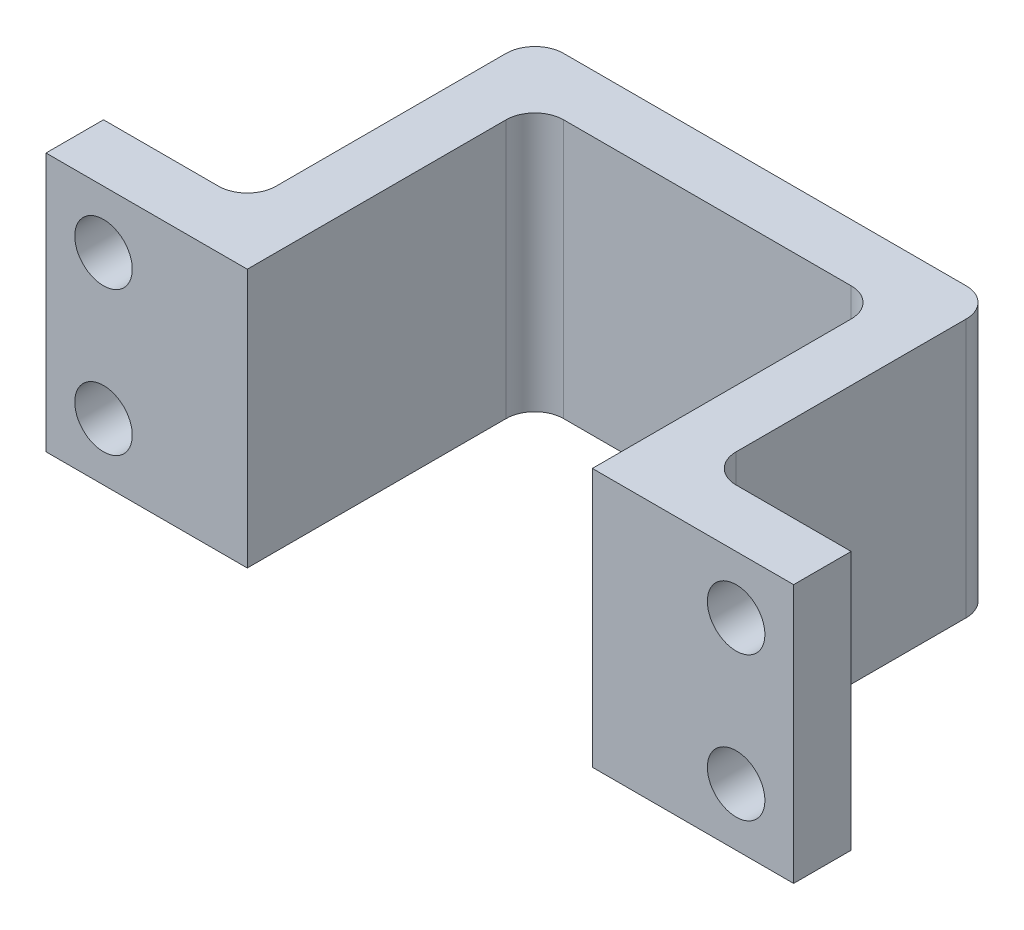
SolidWorks part; units mm, degrees
ref_plane "Front Plane" through (0, 0, 0) normal (0, 0, 1) x (1, 0, 0)
ref_plane "Top Plane" through (0, 0, 0) normal (0, 1, 0) x (1, 0, 0)
ref_plane "Right Plane" through (0, 0, 0) normal (1, 0, 0) x (0, 0, -1)
sketch "Sketch1" plane through (0, 0, 0) normal (0, 1, 0) x (1, 0, 0)
  line L0 (12, 0) -> (13.3184, 0)
  line L2 (0, 0) -> (0, 9)
  line L3 (1, 10) -> (11, 10)
  line L4 (12, 0) -> (12, 9)
  line L5 (-0.2377, 0) -> (0, 0)
  line L6 (-2, 3) -> (-2, 11)
  line L7 (-1, 12) -> (13, 12)
  line L8 (14, 3) -> (14, 11)
  line L10 (-0.2377, 0) -> (-7, 0)
  line L12 (-3, 2) -> (-7, 2)
  line L13 (-7, 0) -> (-7, 2)
  line L14 (13.3184, 0) -> (19, 0)
  line L16 (15, 2) -> (19, 2)
  line L17 (19, 0) -> (19, 2)
  arc A0 (14, 3) -> (15, 2) centre (15, 3) ccw
  arc A1 (-2, 3) -> (-3, 2) centre (-3, 3) cw
  arc A2 (0, 9) -> (1, 10) centre (1, 9) cw
  arc A3 (11, 10) -> (12, 9) centre (11, 9) cw
  arc A4 (13, 12) -> (14, 11) centre (13, 11) cw
  arc A5 (-2, 11) -> (-1, 12) centre (-1, 11) cw
  point P15 (-3.6188, 0)
  point P18 (14, 2)
  point P21 (-2, 2)
  point P24 (0, 10)
  point P27 (12, 10)
  dimension "D10" = 1
  dimension "D1" = 12
  dimension "D2" = 10
  dimension "D3" = 2
  dimension "D4" = 2
  dimension "D5" = 2
  dimension "D6" = 2
  dimension "D7" = 2
  dimension "D8" = 5
  dimension "D9" = 5
extrude "Boss-Extrude1" add sketch "Sketch1" along normal blind 9
sketch "Sketch2" plane through (0, 0, -2) normal (0, 0, -1) x (-1, 0, 0)
  line L0 (-19, 9) -> (-15, 9) construction
  line L1 (-19, 9) -> (-19, 0) construction
  line L2 (-19, 0) -> (-15, 0) construction
  line L3 (3, 9) -> (7, 9) construction
  line L4 (7, 9) -> (7, 0) construction
  line L5 (3, 0) -> (7, 0) construction
  circle A0 centre (-17, 7) radius 1
  circle A1 centre (5, 7) radius 1
  circle A2 centre (-17, 2) radius 1
  circle A3 centre (5, 2) radius 1
  dimension "D1" = 2
  dimension "D2" = 2
  dimension "D6" = 2
  dimension "D7" = 2
  dimension "D9" = 2
  dimension "D10" = 2
  dimension "D11" = 2
  dimension "D12" = 2
  dimension "D3" = 2
  dimension "D4" = 2
  dimension "D5" = 2
  dimension "D8" = 2
extrude "Cut-Extrude1" cut sketch "Sketch2" against normal blind 9
